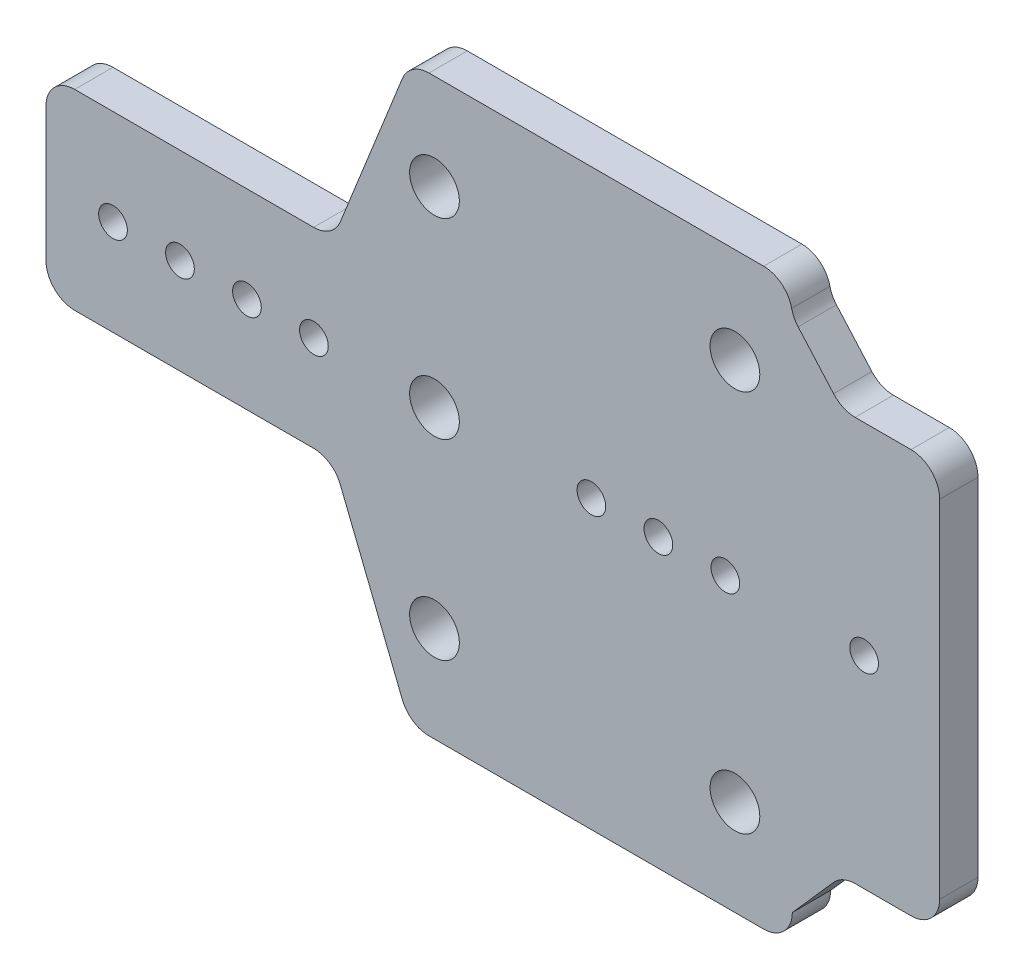
SolidWorks part; units mm, degrees
ref_plane "Front Plane" through (0, 0, 0) normal (0, 0, 1) x (1, 0, 0)
ref_plane "Top Plane" through (0, 0, 0) normal (0, 1, 0) x (1, 0, 0)
ref_plane "Right Plane" through (0, 0, 0) normal (1, 0, 0) x (0, 0, -1)
sketch "Sketch1" plane through (0, 0, 0) normal (0, 0, 1) x (1, 0, 0)
  line L0 (39, 10) -> (39, 30)
  line L2 (-39, -10) -> (-39, 10)
  line L4 (39, -10) -> (39, 10)
  line L5 (-39, -10) -> (39, 10) construction
  line L6 (-39, 10) -> (39, -10) construction
  line L7 (39, 30) -> (-1, 30)
  line L8 (-39, 10) -> (-9, 10)
  line L9 (-9, 10) -> (-1, 30)
  line L10 (-39, -10) -> (-9, -10)
  line L11 (39, -10) -> (39, -30)
  line L12 (39, -30) -> (-1, -30)
  line L13 (-1, -30) -> (-9, -10)
  point P0 (0, 0)
  dimension "D1" = 20
  dimension "D2" = 78
  dimension "D3" = 20
  dimension "D4" = 40
  dimension "D5" = 30
  dimension "D6" = 20
extrude "Boss-Extrude1" add sketch "Sketch1" along normal blind 4
fillet "Fillet1" radius 3 8 edges at (-39, 10, 2) (-1, 30, 2) (-9, 10, 2) (39, 30, 2) (39, -30, 2) (-1, -30, 2) (-9, -10, 2) (-39, -10, 2)
sketch "Sketch3" plane through (0, 0, 4) normal (0, 0, 1) x (1, 0, 0)
  line L0 (39, -27) -> (39, 27) construction
  line L1 (36, 30) -> (1.0311, 30) construction
  line L2 (1.0311, -30) -> (36, -30) construction
  circle A0 centre (33, 20) radius 2.6
  circle A1 centre (1.6, 20) radius 2.6
  circle A2 centre (33, -20) radius 2.6
  circle A3 centre (1.6, -20) radius 2.6
  circle A4 centre (1.6, 0) radius 2.6
  dimension "D1" = 5.2
  dimension "D2" = 6
  dimension "D3" = 10
  dimension "D4" = 10
  dimension "D5" = 5.2
  dimension "D6" = 31.4
  dimension "D7" = 5.2
  dimension "D9" = 6
  dimension "D10" = 5.2
  dimension "D11" = 5.2
  dimension "D8" = 10
extrude "Cut-Extrude1" cut sketch "Sketch3" against normal blind 4
sketch "Sketch4" plane through (0, 0, 4) normal (0, 0, 1) x (1, 0, 0)
  line L0 (-39, 7) -> (-39, -7) construction
  line L1 (39, -27) -> (39, 27) construction
  circle A0 centre (-32, 0) radius 1.5
  circle A1 centre (-25, 0) radius 1.5
  circle A2 centre (-18, 0) radius 1.5
  circle A3 centre (-11, 0) radius 1.5
  circle A4 centre (32, 0) radius 1.5
  circle A5 centre (25, 0) radius 1.5
  circle A6 centre (18, 0) radius 1.5
  dimension "D1" = 3
  dimension "D3" = 3
  dimension "D4" = 7
  dimension "D5" = 3
  dimension "D6" = 7
  dimension "D7" = 3
  dimension "D8" = 7
  dimension "D9" = 3
  dimension "D10" = 7
  dimension "D11" = 3
  dimension "D12" = 7
  dimension "D13" = 3
  dimension "D14" = 7
  dimension "D2" = 7
extrude "Cut-Extrude2" cut sketch "Sketch4" against normal blind 4
sketch "Sketch5" plane through (0, 0, 4) normal (0, 0, 1) x (1, 0, 0)
  line L0 (39, -27) -> (39, 27) construction
  line L1 (39, 10) -> (54, 10)
  line L2 (39, 10) -> (39, -10)
  line L3 (39, -10) -> (54, -10)
  line L4 (54, 10) -> (54, -10)
  dimension "D1" = 15
extrude "Boss-Extrude2" add sketch "Sketch5" against normal blind 4
sketch "Sketch6" plane through (0, 0, 4) normal (0, 0, 1) x (1, 0, 0)
  line L0 (39, 10) -> (54, 10)
  line L1 (54, 10) -> (39, 27)
  line L2 (39, 27) -> (39, 10)
  line L3 (54, -10) -> (39, -10)
  line L4 (39, -10) -> (39, -27)
  line L5 (39, -27) -> (54, -10)
extrude "Boss-Extrude3" add sketch "Sketch6" against normal blind 4
sketch "Sketch7" plane through (0, 0, 4) normal (0, 0, 1) x (1, 0, 0)
  line L0 (54, -10) -> (54, 10) construction
  circle A0 centre (46.5, 0) radius 1.5
  dimension "D1" = 3
  dimension "D2" = 7.5
extrude "Cut-Extrude3" cut sketch "Sketch7" against normal blind 4
sketch "Sketch8" plane through (0, 0, 4) normal (0, 0, 1) x (1, 0, 0)
  line L0 (54, -10) -> (54, 10) construction
  line L1 (54, -21.1) -> (96.2, -21.1)
  line L2 (54, -21.1) -> (54, 21.1)
  line L3 (54, 21.1) -> (96.2, 21.1)
  line L4 (96.2, -21.1) -> (96.2, 21.1)
  line L5 (54, -21.1) -> (96.2, 21.1) construction
  line L6 (54, 21.1) -> (96.2, -21.1) construction
  line L7 (54, 21.1) -> (44.2059, 21.1)
  line L8 (54, 10) -> (39, 27) construction
  line L9 (44.2059, 21.1) -> (54, 10)
  line L10 (54, 10) -> (54, 21.1)
  line L11 (54, -21.1) -> (44.2059, -21.1)
  line L12 (39, -27) -> (54, -10) construction
  line L13 (44.2059, -21.1) -> (54, -10)
  line L14 (54, -10) -> (54, -21.1)
  point P0 (75.1, 0)
  line M12 (54, 10) -> (39, 27)
  line M28 (39, -27) -> (54, -10)
  line M29 (54, -10) -> (54, 10)
  dimension "D1" = 42.2
  dimension "D2" = 42.2
  dimension "D3" = 0
extrude "Boss-Extrude4" add sketch "Sketch8" against normal blind 4 contours L1 L4 L3 L2 M29 | L2 L7 M12 | L11 L2 M28
sketch "Sketch10" plane through (0, 0, 4) normal (0, 0, 1) x (1, 0, 0)
  line L0 (96.2, -21.1) -> (96.2, 21.1) construction
  circle A0 centre (74.8, 0) radius 11.5
  dimension "D1" = 23
  dimension "D2" = 21.4
extrude "Cut-Extrude4" cut sketch "Sketch10" against normal blind 4
sketch "Sketch14" plane through (0, 0, 4) normal (0, 0, 1) x (1, 0, 0)
  circle A0 centre (90.6745, 15.8745) radius 1.5
  circle A1 centre (58.9255, -15.8745) radius 1.5
  circle A2 centre (58.9255, 15.8745) radius 1.5
  circle A3 centre (90.6745, -15.8745) radius 1.5
  dimension "D2" = 3
  dimension "D3" = 3
  dimension "D4" = 3
  dimension "D5" = 3
extrude "Cut-Extrude5" cut sketch "Sketch14" against normal blind 4
fillet "Fillet2" radius 3 5 edges at (39, 27, 2) (44.2059, 21.1, 2) (96.2, 21.1, 2) (96.2, -21.1, 2) (44.2059, -21.1, 2)
sketch "Sketch17" plane through (0, 0, 4) normal (0, 0, 1) x (1, 0, 0)
  line L0 (45.5597, 21.1) -> (93.2, 21.1) construction
  line L1 (54.4032, 21.1) -> (96.2, 21.1)
  line L2 (54.4032, 21.1) -> (54.4032, -21.1)
  line L3 (54.4032, -21.1) -> (96.2, -21.1)
  line L4 (96.2, 21.1) -> (96.2, -21.1)
extrude "Cut-Extrude6" cut sketch "Sketch17" against normal blind 10
fillet "Fillet3" radius 3 2 edges at (54.4032, 21.1, 2) (54.4032, -21.1, 2)
